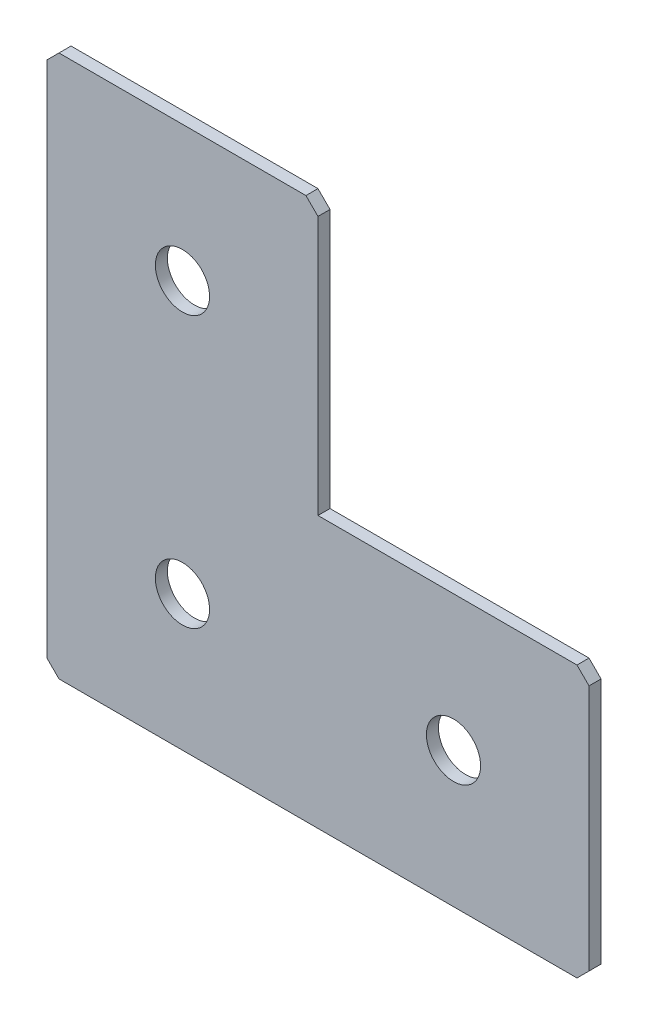
SolidWorks part; units mm, degrees
material "Простая углеродистая сталь"
ref_plane "Спереди(Плоскость XY)" through (0, 0, 0) normal (0, 0, 1) x (1, 0, 0)
ref_plane "Сверху(Плоскость XZ)" through (0, 0, 0) normal (0, 1, 0) x (1, 0, 0)
ref_plane "Справа(Плоскость ZY)" through (0, 0, 0) normal (1, 0, 0) x (0, 0, -1)
sketch "Эскиз1" plane through (0, 0, 0) normal (0, 0, -1) x (1, 0, 0)
  line L0 (0, 0) -> (0, 90)
  line L1 (0, 90) -> (90, 90)
  line L2 (90, 90) -> (90, 45)
  line L3 (90, 45) -> (45, 45)
  line L4 (45, 45) -> (45, 0)
  line L5 (45, 0) -> (0, 0)
  dimension "D1" = 90
  dimension "D2" = 45
  dimension "D3" = 45
  dimension "D4" = 45
extrude "Бобышка-Вытянуть1" add sketch "Эскиз1" along normal blind 2
hole_wizard "Отверстие с зазором M81" positions "Эскиз2" profile "Эскиз3" hole size "M8" standard "DIN" end condition through all
sketch "Эскиз2" plane through (0, 0, -2) normal (0, 0, -1) x (1, 0, 0)
  line L1 (0, 0) -> (45, 0) construction
  line L6 (0, 90) -> (0, 0) construction
  point P4 (22.5, 67.5)
  point P6 (22.5, 22.5)
  point P29 (67.5, 67.5)
  dimension "D1" = 45
  dimension "D2" = 45
  dimension "D4" = 22.5
  dimension "D5" = 22.5
sketch "Эскиз3" plane through (22.5, -67.5, -2) normal (1, 0, 0) x (0, 1, 0)
  line L0 (0, 0) -> (0, 2)
  line L1 (0, 2) -> (4.5, 2)
  line L2 (4.5, 2) -> (4.5, 0)
  line L5 (4.5, 0) -> (0, 0)
  line L11 (0, -6.35) -> (0, 107.95) construction
  dimension "Диаметр сквозного отверстия" = 9
  dimension "Глубина сквозного отверстия" = 2
chamfer "Фаска1" distance 2 angle 45 5 edges at (0, 0, -1) (45, 0, -1) (90, -45, -1) (90, -90, -1) (0, -90, -1)
